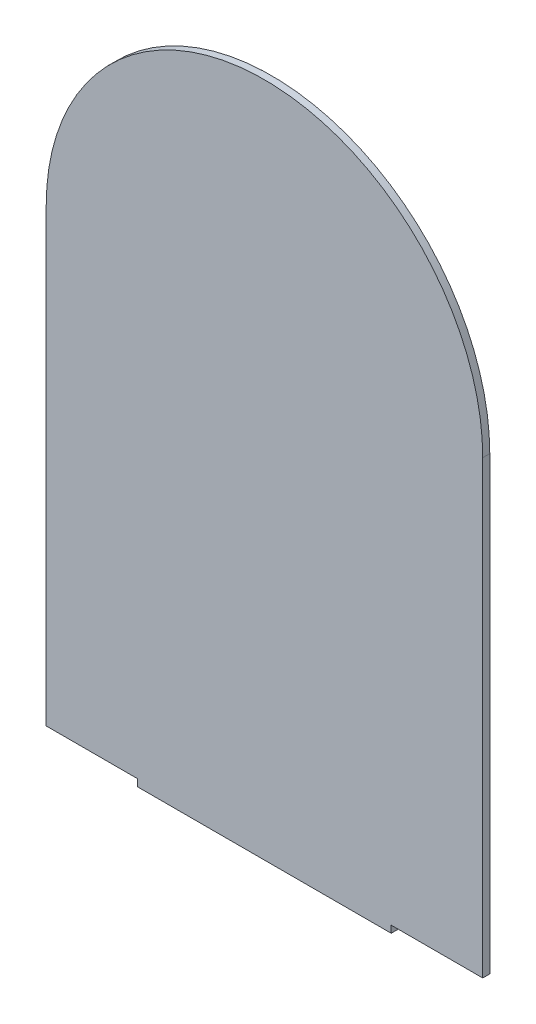
SolidWorks part; units mm, degrees
ref_plane "Front" through (0, 0, 0) normal (0, 0, 1) x (1, 0, 0)
ref_plane "Top" through (0, 0, 0) normal (0, 1, 0) x (1, 0, 0)
ref_plane "Right" through (0, 0, 0) normal (1, 0, 0) x (0, 0, -1)
sketch "Sketch2" plane through (0, 0, 0) normal (0, 0, 1) x (1, 0, 0)
  line L0 (0, 203.2) -> (0, 0)
  line L1 (0, 0) -> (41.275, 0)
  line L2 (196.85, 0) -> (196.85, 203.2)
  line L3 (155.575, 0) -> (196.85, 0)
  line L5 (41.275, 0) -> (41.275, -3.175)
  line L6 (41.275, -3.175) -> (155.575, -3.175)
  line L7 (155.575, 0) -> (155.575, -3.175)
  arc A0 (0, 203.2) -> (196.85, 203.2) centre (98.425, 203.2) cw
  dimension "D1" = 196.85
  dimension "D2" = 203.2
  dimension "D3" = 114.3
  dimension "D4" = 3.175
  dimension "D5" = 41.275
extrude "Boss-Extrude1" add sketch "Sketch2" along normal blind 3.175
